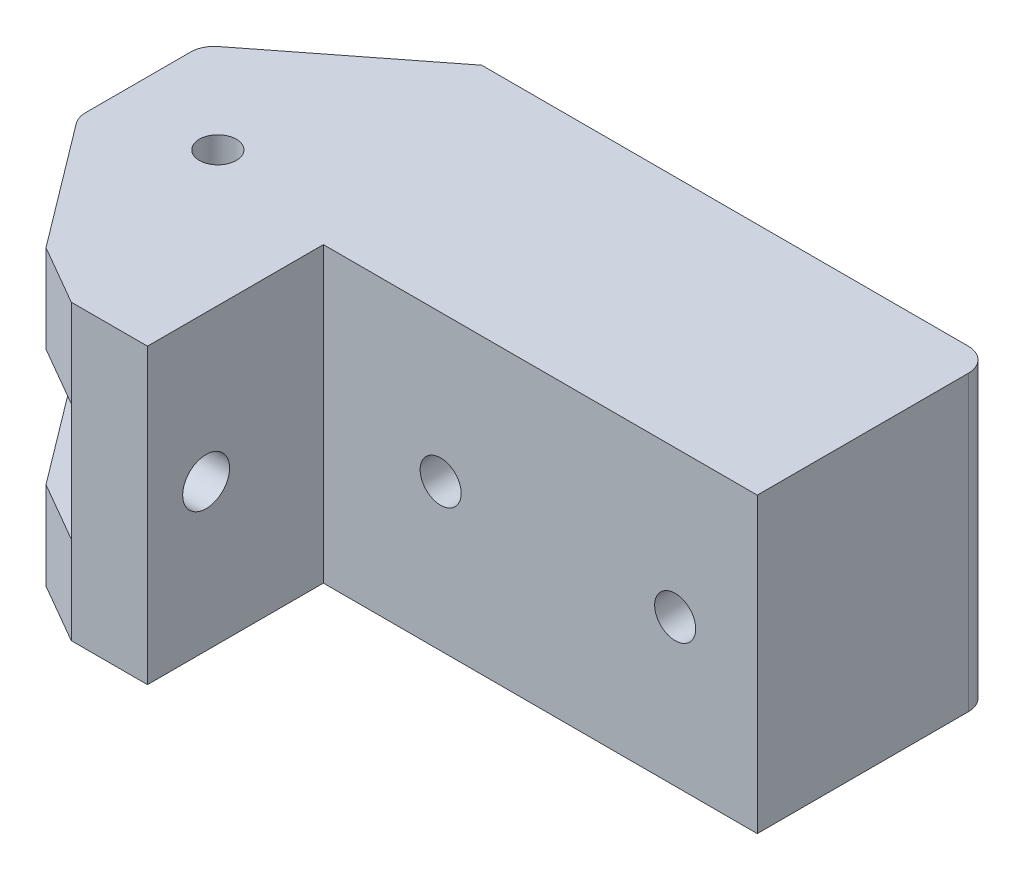
SolidWorks part; units mm, degrees
ref_plane "Front Plane" through (0, 0, 0) normal (0, 0, 1) x (1, 0, 0)
ref_plane "Top Plane" through (0, 0, 0) normal (0, 1, 0) x (1, 0, 0)
ref_plane "Right Plane" through (0, 0, 0) normal (1, 0, 0) x (0, 0, -1)
sketch "Sketch1" plane through (0, 0, 0) normal (0, 1, 0) x (1, 0, 0)
  line L0 (0, 0) -> (-43.5, 0)
  line L1 (-43.5, 0) -> (-43.5, -35) construction
  line L2 (-43.5, -35) -> (-37, -35)
  line L3 (-37, -35) -> (-37, -20)
  line L4 (-37, -20) -> (0, -20)
  line L5 (0, -20) -> (0, 0)
  line L6 (-43.5, 0) -> (-56.8853, -10.4577)
  line L7 (-56.8853, -10.4577) -> (-56.8853, -21.0577)
  line L8 (-56.8853, -21.0577) -> (-48.5962, -32.0577)
  line L9 (-48.5962, -32.0577) -> (-43.5, -35)
  line L10 (-43.5, -17.5) -> (-48.5, -17.5) construction
  circle A0 centre (-48.5, -17.5) radius 1.575
  dimension "D11" = 3.15
  dimension "D1" = 43.5
  dimension "D2" = 35
  dimension "D3" = 20
  dimension "D4" = 37
  dimension "D5" = 30
  dimension "D6" = 38
  dimension "D7" = 10.6
  dimension "D8" = 37
  dimension "D9" = 11
  dimension "D10" = 5
extrude "Boss-Extrude1" add sketch "Sketch1" along normal mid plane 25
sketch "Sketch2" plane through (0, 0, 35) normal (0, 0, 1) x (1, 0, 0)
  line L0 (-43.5, 12.5) -> (-43.5, -12.5) construction
  line L1 (-43.5, -5) -> (-56.8853, -5)
  line L2 (-43.5, -5) -> (-43.5, 5)
  line L3 (-43.5, 5) -> (-56.8853, 5)
  line L4 (-56.8853, -5) -> (-56.8853, 5)
  line L5 (-56.8853, 12.5) -> (-56.8853, -12.5) construction
  line L6 (-56.8853, 12.5) -> (-48.5962, 12.5) construction
  dimension "D1" = 7.5
  dimension "D2" = 10
extrude "Cut-Extrude1" cut sketch "Sketch2" against normal through all
sketch "Sketch3" plane through (0, 0, 20) normal (0, 0, 1) x (1, 0, 0)
  line L1 (0, 0) -> (-27, 0) construction
  line L2 (-37, 12.5) -> (-37, -12.5) construction
  circle A0 centre (-27, 0) radius 1.75
  circle A1 centre (-7, 0) radius 1.75
  dimension "D1" = 3.5
  dimension "D2" = 20
  dimension "D3" = 10
extrude "Cut-Extrude2" cut sketch "Sketch3" against normal blind 25
sketch "Sketch4" plane through (0, 0, 0) normal (0, 0, -1) x (-1, 0, 0)
  circle A0 centre (7, 0) radius 4
  circle A2 centre (27, 0) radius 4
extrude "Cut-Extrude3" cut sketch "Sketch4" against normal blind 4
fillet "Fillet1" radius 2 5 edges at (0, 0, 0) (-56.8853, 8.75, 10.4577) (-56.8853, 8.75, 21.0577) (-56.8853, -8.75, 21.0577) (-56.8853, -8.75, 10.4577)
sketch "Sketch5" plane through (-43.5, 0, 0) normal (-1, 0, 0) x (0, 0, 1)
  line L0 (30, -12.5) -> (30, 12.5) construction
  line L3 (35, -5) -> (35, 5) construction
  line L4 (21.5922, 12.5) -> (32.0577, 12.5) construction
  line L5 (21.5922, -12.5) -> (32.0577, -12.5) construction
  circle A0 centre (30, 0) radius 2
  dimension "D1" = 4
  dimension "D2" = 5
sketch "Sketch6" plane through (0, 12.5, 0) normal (0, 1, 0) x (1, 0, 0)
  line L0 (-37, -35) -> (-37, -20)
extrude "Cut-Extrude4" cut sketch "Sketch5" against normal blind 10
sketch "Sketch7" plane through (-43.5, 0, 0) normal (-1, 0, 0) x (0, 0, 1)
  circle A0 centre (30, 0) radius 3.575
  dimension "D1" = 7.15
extrude "Cut-Extrude5" cut sketch "Sketch7" against normal blind 3.5
ref_plane "Plane1" through (0, 0, 0) normal (0, 1, 0) x (1, 0, 0)
sketch "Sketch8" plane through (0, 0, 0) normal (0, 1, 0) x (1, 0, 0)
  circle A0 centre (-48.5, -17.5) radius 10
extrude "Cut-Extrude6" cut sketch "Sketch8" against normal blind 5 and the other way blind 5
sketch "Sketch9" plane through (0, -12.5, 0) normal (0, -1, 0) x (1, 0, 0)
  line L1 (-46.8006, 14.4814) -> (-45.0361, 17.4624)
  line L2 (-45.0361, 17.4624) -> (-46.7355, 20.481)
  line L3 (-46.7355, 20.481) -> (-50.1994, 20.5186)
  line L4 (-50.1994, 20.5186) -> (-51.9639, 17.5376)
  line L5 (-51.9639, 17.5376) -> (-50.2645, 14.519)
  line L6 (-50.2645, 14.519) -> (-46.8006, 14.4814)
  circle A0 centre (-48.5, 17.5) radius 3 construction
extrude "Cut-Extrude7" cut sketch "Sketch9" against normal blind 3 contours L6 L1 L2 L3 L4 L5
